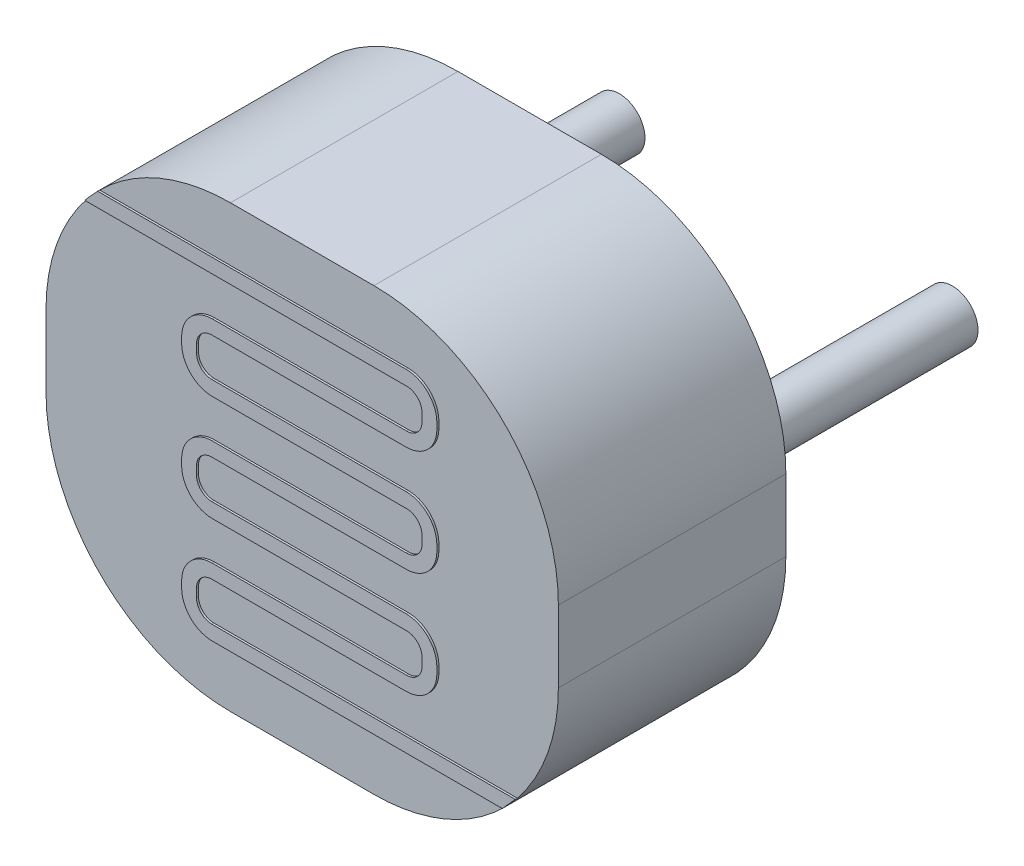
SolidWorks part; units mm, degrees
ref_plane "Front Plane" through (0, 0, 0) normal (0, 0, 1) x (1, 0, 0)
ref_plane "Top Plane" through (0, 0, 0) normal (0, 1, 0) x (1, 0, 0)
ref_plane "Right Plane" through (0, 0, 0) normal (1, 0, 0) x (0, 0, -1)
sketch "Sketch1" plane through (0, 0, 0) normal (0, 0, 1) x (1, 0, 0)
  line L1 (-6.3986, 5.507) -> (-4.9986, 5.507)
  line L2 (-8.1986, 3.707) -> (-8.1986, 3.007)
  line L3 (-6.3986, 1.207) -> (-4.9986, 1.207)
  line L4 (-3.1986, 3.707) -> (-3.1986, 3.007)
  arc A0 (-6.3986, 5.507) -> (-8.1986, 3.707) centre (-6.3986, 3.707) ccw
  arc A1 (-8.1986, 3.007) -> (-6.3986, 1.207) centre (-6.3986, 3.007) ccw
  arc A2 (-4.9986, 1.207) -> (-3.1986, 3.007) centre (-4.9986, 3.007) ccw
  arc A3 (-4.9986, 5.507) -> (-3.1986, 3.707) centre (-4.9986, 3.707) cw
  point P6 (-8.1986, 5.507)
  point P9 (-8.1986, 1.207)
  point P14 (-3.1986, 5.507)
  dimension "D1" = 5
  dimension "D2" = 4.3
  dimension "D3" = 1.8
extrude "Extrude1" add sketch "Sketch1" along normal blind 2.22
sketch "Sketch2" plane through (0, 0, 0) normal (0, 0, -1) x (-1, 0, 0)
  line L0 (4.0736, 3.357) -> (7.3236, 3.357) construction
  line L1 (6.3986, 1.207) -> (4.9986, 1.207) construction
  line L2 (4.9986, 5.507) -> (6.3986, 5.507) construction
  line L7 (6.3986, 5.507) -> (4.9986, 5.507)
  line L8 (3.1986, 3.707) -> (3.1986, 3.007)
  line L9 (4.9986, 1.207) -> (6.3986, 1.207)
  line L10 (8.1986, 3.007) -> (8.1986, 3.707)
  line L11 (6.3986, 5.507) -> (5.6986, 5.507)
  line L13 (5.6986, 1.207) -> (6.3986, 1.207)
  line L14 (8.1986, 3.007) -> (8.1986, 3.707)
  circle A0 centre (4.0736, 3.357) radius 0.25
  circle A1 centre (7.3236, 3.357) radius 0.25
  arc A4 (8.1986, 3.707) -> (6.3986, 5.507) centre (6.3986, 3.707) ccw
  arc A5 (4.9986, 5.507) -> (3.1986, 3.707) centre (4.9986, 3.707) ccw
  arc A6 (3.1986, 3.007) -> (4.9986, 1.207) centre (4.9986, 3.007) ccw
  arc A7 (6.3986, 1.207) -> (8.1986, 3.007) centre (6.3986, 3.007) ccw
  arc A8 (8.1986, 3.707) -> (6.3986, 5.507) centre (6.3986, 3.707) ccw
  arc A11 (6.3986, 1.207) -> (8.1986, 3.007) centre (6.3986, 3.007) ccw
  point P6 (5.6986, 3.357)
  point P23 (8.1986, 3.357)
  dimension "D4" = 0.5
  dimension "D5" = 0.5
  dimension "D2" = 3.25
  dimension "D1" = 0
sketch "Sketch3" plane through (0, 0, 2.22) normal (0, 0, 1) x (1, 0, 0)
  line L0 (-4.6591, 4.837) -> (-7.7997, 4.837)
  line L1 (-6.5602, 1.875) -> (-3.5991, 1.875)
  line L2 (-7.7997, 4.837) -> (-7.7575, 4.8875)
  line L3 (-7.7575, 4.8875) -> (-7.6742, 4.977)
  line L4 (-6.555, 1.7342) -> (-3.7258, 1.7342)
  line L5 (-3.7258, 1.7342) -> (-3.5991, 1.875)
  line L14 (-4.5091, 4.687) -> (-4.5091, 4.6077)
  line L15 (-4.6591, 4.4577) -> (-6.555, 4.4577)
  line L16 (-6.855, 4.1577) -> (-6.855, 4.1017)
  line L17 (-6.555, 3.8017) -> (-4.6591, 3.8017)
  line L18 (-4.5091, 3.6517) -> (-4.5091, 3.5757)
  line L19 (-4.6591, 3.4257) -> (-6.555, 3.4257)
  line L21 (-6.855, 3.1257) -> (-6.855, 3.0697)
  line L22 (-6.555, 2.7697) -> (-4.6591, 2.7697)
  line L23 (-4.5091, 2.6197) -> (-4.5091, 2.5437)
  line L24 (-4.6591, 2.3937) -> (-6.555, 2.3937)
  line L25 (-6.855, 2.0937) -> (-6.855, 2.0342)
  line L28 (-7.6742, 4.977) -> (-4.6644, 4.977)
  line L29 (-4.3644, 4.677) -> (-4.3644, 4.6191)
  line L30 (-4.6644, 4.3191) -> (-6.5602, 4.3191)
  line L31 (-6.7102, 4.1691) -> (-6.7102, 4.0931)
  line L32 (-6.5602, 3.9431) -> (-4.6644, 3.9431)
  line L33 (-4.3644, 3.6431) -> (-4.3644, 3.5871)
  line L34 (-4.6644, 3.2871) -> (-6.5602, 3.2871)
  line L35 (-6.7102, 3.1371) -> (-6.7102, 3.0611)
  line L36 (-6.5602, 2.9111) -> (-4.6644, 2.9111)
  line L37 (-4.3644, 2.6111) -> (-4.3644, 2.5551)
  line L38 (-4.6644, 2.2551) -> (-6.5602, 2.2551)
  line L39 (-6.7102, 2.1051) -> (-6.7102, 2.025)
  arc A0 (-4.6591, 4.837) -> (-4.5091, 4.687) centre (-4.6591, 4.687) cw
  arc A1 (-6.3986, 5.507) -> (-8.1986, 3.707) centre (-6.3986, 3.707) ccw construction
  arc A2 (-4.9986, 1.207) -> (-3.1986, 3.007) centre (-4.9986, 3.007) ccw construction
  arc A3 (-4.5091, 4.6077) -> (-4.6591, 4.4577) centre (-4.6591, 4.6077) cw
  arc A4 (-6.5602, 4.3191) -> (-6.7102, 4.1691) centre (-6.5602, 4.1691) ccw
  arc A5 (-6.7102, 4.0931) -> (-6.5602, 3.9431) centre (-6.5602, 4.0931) ccw
  arc A6 (-4.6591, 3.8017) -> (-4.5091, 3.6517) centre (-4.6591, 3.6517) cw
  arc A7 (-4.5091, 3.5757) -> (-4.6591, 3.4257) centre (-4.6591, 3.5757) cw
  arc A8 (-6.5602, 3.2871) -> (-6.7102, 3.1371) centre (-6.5602, 3.1371) ccw
  arc A9 (-6.7102, 3.0611) -> (-6.5602, 2.9111) centre (-6.5602, 3.0611) ccw
  arc A10 (-4.6591, 2.7697) -> (-4.5091, 2.6197) centre (-4.6591, 2.6197) cw
  arc A11 (-4.5091, 2.5437) -> (-4.6591, 2.3937) centre (-4.6591, 2.5437) cw
  arc A12 (-6.5602, 2.2551) -> (-6.7102, 2.1051) centre (-6.5602, 2.1051) ccw
  arc A13 (-6.7102, 2.025) -> (-6.5602, 1.875) centre (-6.5602, 2.025) ccw
  arc A14 (-4.6644, 4.977) -> (-4.3644, 4.677) centre (-4.6644, 4.677) cw
  arc A15 (-4.3644, 4.6191) -> (-4.6644, 4.3191) centre (-4.6644, 4.6191) cw
  arc A16 (-6.555, 4.4577) -> (-6.855, 4.1577) centre (-6.555, 4.1577) ccw
  arc A17 (-6.855, 4.1017) -> (-6.555, 3.8017) centre (-6.555, 4.1017) ccw
  arc A18 (-4.6644, 3.9431) -> (-4.3644, 3.6431) centre (-4.6644, 3.6431) cw
  arc A19 (-4.3644, 3.5871) -> (-4.6644, 3.2871) centre (-4.6644, 3.5871) cw
  arc A20 (-6.555, 3.4257) -> (-6.855, 3.1257) centre (-6.555, 3.1257) ccw
  arc A21 (-6.855, 3.0697) -> (-6.555, 2.7697) centre (-6.555, 3.0697) ccw
  arc A22 (-4.6644, 2.9111) -> (-4.3644, 2.6111) centre (-4.6644, 2.6111) cw
  arc A23 (-4.3644, 2.5551) -> (-4.6644, 2.2551) centre (-4.6644, 2.5551) cw
  arc A24 (-6.555, 2.3937) -> (-6.855, 2.0937) centre (-6.555, 2.0937) ccw
  arc A25 (-6.855, 2.0342) -> (-6.555, 1.7342) centre (-6.555, 2.0342) ccw
  dimension "D1" = 0.15
  dimension "D2" = 0.15
  dimension "D3" = 0.3
extrude "Extrude6" add sketch "Sketch3" along normal blind 0.02 contours L5 L4 A25 L25 A24 L24 A11 L23 A10 L22 A21 L21 A20 L19 A7 L18 A6 L17 A17 L16 A16 L15 A3 L14 A0 L0 L2 L3 L28 A14 L29 A15 L30 A4 L31 A5 L32 A18 L33 A19 L34 A8 L35 A9 L36 A22 L37 A23 L38 A12 L39 A13 L1
extrude "Extrude7" add sketch "Sketch2" along normal blind 2.5 contours A0 | A1
